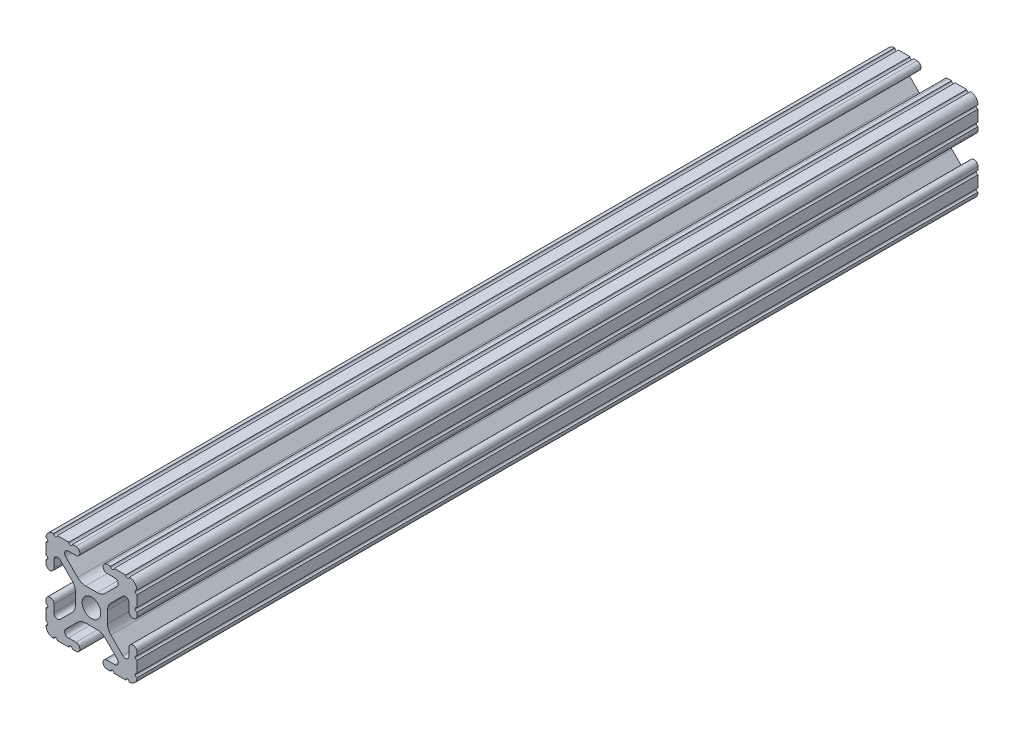
SolidWorks part; units mm, degrees
material "6061-T6 (SS)"
ref_plane "Front Plane" through (0, 0, 0) normal (0, 0, 1) x (1, 0, 0)
ref_plane "Top Plane" through (0, 0, 0) normal (0, 1, 0) x (1, 0, 0)
ref_plane "Right Plane" through (0, 0, 0) normal (1, 0, 0) x (0, 0, -1)
ref_plane "Plane1" through (0, 0, -450.85) normal (0, 0, -1) x (-1, 0, 0)
sketch "Sketch1" plane through (0, 0, -450.85) normal (0, 0, -1) x (-1, 0, 0)
  line L0 (12.7, -9.5504) -> (12.7, -6.3331)
  line L1 (12.7, -5.3171) -> (12.7, -4.3434)
  line L2 (10.4902, -4.3434) -> (10.4902, -6.4748)
  line L3 (8.7558, -7.1932) -> (5.4257, -3.8632)
  line L4 (4.4958, -1.6181) -> (4.4958, 1.6181)
  line L5 (5.4257, 3.8632) -> (8.7558, 7.1932)
  line L6 (10.4902, 6.4748) -> (10.4902, 4.3434)
  line L7 (12.7, 4.3434) -> (12.7, 5.3171)
  line L8 (12.7, 6.3331) -> (12.7, 9.5504)
  line L9 (9.5504, 12.7) -> (6.3331, 12.7)
  line L10 (5.3171, 12.7) -> (4.3434, 12.7)
  line L11 (4.3434, 10.4902) -> (6.4748, 10.4902)
  line L12 (7.1932, 8.7558) -> (3.8632, 5.4257)
  line L13 (1.6181, 4.4958) -> (-1.6181, 4.4958)
  line L14 (-3.8632, 5.4257) -> (-7.1932, 8.7558)
  line L15 (-6.4748, 10.4902) -> (-4.3434, 10.4902)
  line L16 (-4.3434, 12.7) -> (-5.3171, 12.7)
  line L17 (-6.3331, 12.7) -> (-9.5504, 12.7)
  line L18 (-12.7, 9.5504) -> (-12.7, 6.3331)
  line L19 (-12.7, 5.3171) -> (-12.7, 4.3434)
  line L20 (-10.4902, 4.3434) -> (-10.4902, 6.4748)
  line L21 (-8.7558, 7.1932) -> (-5.4257, 3.8632)
  line L22 (-4.4958, 1.6181) -> (-4.4958, -1.6181)
  line L23 (-5.4257, -3.8632) -> (-8.7558, -7.1932)
  line L24 (-10.4902, -6.4748) -> (-10.4902, -4.3434)
  line L25 (-12.7, -4.3434) -> (-12.7, -5.3171)
  line L26 (-12.7, -6.3331) -> (-12.7, -9.5504)
  line L27 (-9.5504, -12.7) -> (-6.3331, -12.7)
  line L28 (-5.3171, -12.7) -> (-4.3434, -12.7)
  line L29 (-4.3434, -10.4902) -> (-6.4748, -10.4902)
  line L30 (-7.1932, -8.7558) -> (-3.8632, -5.4257)
  line L31 (-1.6181, -4.4958) -> (1.6181, -4.4958)
  line L32 (3.8632, -5.4257) -> (7.1932, -8.7558)
  line L33 (6.4748, -10.4902) -> (4.3434, -10.4902)
  line L34 (4.3434, -12.7) -> (5.3171, -12.7)
  line L35 (6.3331, -12.7) -> (9.5504, -12.7)
  arc A0 (12.6998, -10.5664) -> (12.7, -9.5504) centre (12.7, -10.0584) cw
  arc A1 (12.7, -6.3331) -> (12.7, -5.3171) centre (12.7, -5.8251) cw
  arc A2 (12.7, -4.3434) -> (10.4902, -4.3434) centre (11.5951, -4.3434) ccw
  arc A3 (10.4902, -6.4748) -> (8.7558, -7.1932) centre (9.4742, -6.4748) cw
  arc A4 (5.4257, -3.8632) -> (4.4958, -1.6181) centre (7.6708, -1.6181) cw
  arc A5 (4.4958, 1.6181) -> (5.4257, 3.8632) centre (7.6708, 1.6181) cw
  arc A6 (8.7558, 7.1932) -> (10.4902, 6.4748) centre (9.4742, 6.4748) cw
  arc A7 (10.4902, 4.3434) -> (12.7, 4.3434) centre (11.5951, 4.3434) ccw
  arc A8 (12.7, 5.3171) -> (12.7, 6.3331) centre (12.7, 5.8251) cw
  arc A9 (12.7, 9.5504) -> (12.6998, 10.5664) centre (12.7, 10.0584) cw
  arc A10 (12.6998, 10.5664) -> (10.5664, 12.6998) centre (10.5918, 10.5918) ccw
  arc A11 (10.5664, 12.6998) -> (9.5504, 12.7) centre (10.0584, 12.7) cw
  arc A12 (6.3331, 12.7) -> (5.3171, 12.7) centre (5.8251, 12.7) cw
  arc A13 (4.3434, 12.7) -> (4.3434, 10.4902) centre (4.3434, 11.5951) ccw
  arc A14 (6.4748, 10.4902) -> (7.1932, 8.7558) centre (6.4748, 9.4742) cw
  arc A15 (3.8632, 5.4257) -> (1.6181, 4.4958) centre (1.6181, 7.6708) cw
  arc A16 (-1.6181, 4.4958) -> (-3.8632, 5.4257) centre (-1.6181, 7.6708) cw
  arc A17 (-7.1932, 8.7558) -> (-6.4748, 10.4902) centre (-6.4748, 9.4742) cw
  arc A18 (-4.3434, 10.4902) -> (-4.3434, 12.7) centre (-4.3434, 11.5951) ccw
  arc A19 (-5.3171, 12.7) -> (-6.3331, 12.7) centre (-5.8251, 12.7) cw
  arc A20 (-9.5504, 12.7) -> (-10.5664, 12.6998) centre (-10.0584, 12.7) cw
  arc A21 (-10.5664, 12.6998) -> (-12.6998, 10.5664) centre (-10.5918, 10.5918) ccw
  arc A22 (-12.6998, 10.5664) -> (-12.7, 9.5504) centre (-12.7, 10.0584) cw
  arc A23 (-12.7, 6.3331) -> (-12.7, 5.3171) centre (-12.7, 5.8251) cw
  arc A24 (-12.7, 4.3434) -> (-10.4902, 4.3434) centre (-11.5951, 4.3434) ccw
  arc A25 (-10.4902, 6.4748) -> (-8.7558, 7.1932) centre (-9.4742, 6.4748) cw
  arc A26 (-5.4257, 3.8632) -> (-4.4958, 1.6181) centre (-7.6708, 1.6181) cw
  arc A27 (-4.4958, -1.6181) -> (-5.4257, -3.8632) centre (-7.6708, -1.6181) cw
  arc A28 (-8.7558, -7.1932) -> (-10.4902, -6.4748) centre (-9.4742, -6.4748) cw
  arc A29 (-10.4902, -4.3434) -> (-12.7, -4.3434) centre (-11.5951, -4.3434) ccw
  arc A30 (-12.7, -5.3171) -> (-12.7, -6.3331) centre (-12.7, -5.8251) cw
  arc A31 (-12.7, -9.5504) -> (-12.6998, -10.5664) centre (-12.7, -10.0584) cw
  arc A32 (-12.6998, -10.5664) -> (-10.5664, -12.6998) centre (-10.5918, -10.5918) ccw
  arc A33 (-10.5664, -12.6998) -> (-9.5504, -12.7) centre (-10.0584, -12.7) cw
  arc A34 (-6.3331, -12.7) -> (-5.3171, -12.7) centre (-5.8251, -12.7) cw
  arc A35 (-4.3434, -12.7) -> (-4.3434, -10.4902) centre (-4.3434, -11.5951) ccw
  arc A36 (-6.4748, -10.4902) -> (-7.1932, -8.7558) centre (-6.4748, -9.4742) cw
  arc A37 (-3.8632, -5.4257) -> (-1.6181, -4.4958) centre (-1.6181, -7.6708) cw
  arc A38 (1.6181, -4.4958) -> (3.8632, -5.4257) centre (1.6181, -7.6708) cw
  arc A39 (7.1932, -8.7558) -> (6.4748, -10.4902) centre (6.4748, -9.4742) cw
  arc A40 (4.3434, -10.4902) -> (4.3434, -12.7) centre (4.3434, -11.5951) ccw
  arc A41 (5.3171, -12.7) -> (6.3331, -12.7) centre (5.8251, -12.7) cw
  arc A42 (9.5504, -12.7) -> (10.5664, -12.6998) centre (10.0584, -12.7) cw
  arc A43 (10.5664, -12.6998) -> (12.6998, -10.5664) centre (10.5918, -10.5918) ccw
  circle A44 centre (0, 0) radius 2.6035
extrude "Boss-Extrude1" add sketch "Sketch1" against normal mid plane 235.0008
